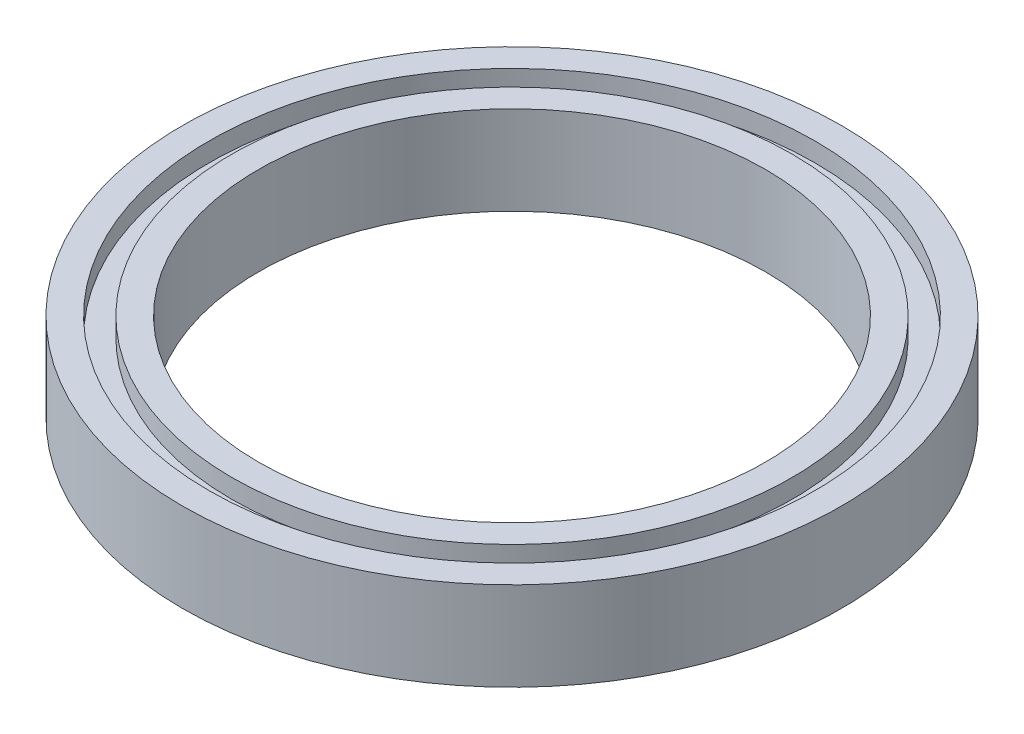
SolidWorks part; units mm, degrees
ref_plane "前视基准面" through (0, 0, 0) normal (0, 0, 1) x (1, 0, 0)
ref_plane "上视基准面" through (0, 0, 0) normal (0, 1, 0) x (1, 0, 0)
ref_plane "右视基准面" through (0, 0, 0) normal (1, 0, 0) x (0, 0, -1)
sketch "草图1" plane through (0, 0, 0) normal (0, 1, 0) x (1, 0, 0)
  circle A0 centre (0, 0) radius 26
  circle A1 centre (0, 0) radius 20
  dimension "D1" = 40
  dimension "D2" = 52
extrude "凸台-拉伸1" add sketch "草图1" along normal blind 7
sketch "草图2" plane through (0, 7, 0) normal (0, 1, 0) x (1, 0, 0)
  circle A0 centre (0, 0) radius 22.1
  circle A1 centre (0, 0) radius 23.9
  dimension "D1" = 1.8
  dimension "D2" = 44.2
extrude "切除-拉伸1" cut sketch "草图2" against normal blind 1.5
ref_plane "基准面1" through (0, 3.5, 0) normal (0, 1, 0) x (1, 0, 0)
mirror "镜向1" about plane through (0, 3.5, 0) normal (0, 1, 0) of "切除-拉伸1"
